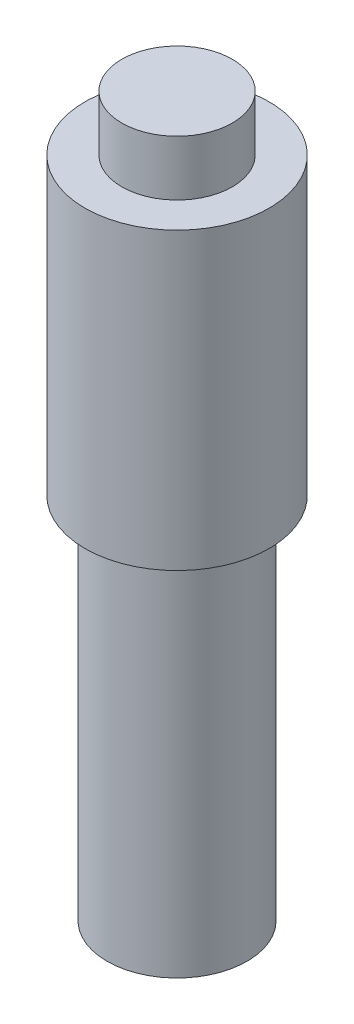
SolidWorks part; units mm, degrees
ref_plane "前基準面" through (0, 0, 0) normal (0, 0, 1) x (1, 0, 0)
ref_plane "上基準面" through (0, 0, 0) normal (0, 1, 0) x (1, 0, 0)
ref_plane "右基準面" through (0, 0, 0) normal (1, 0, 0) x (0, 0, -1)
sketch "草圖1" plane through (0, 0, 0) normal (0, 0, 1) x (1, 0, 0)
  line L0 (0, 46.1554) -> (0, -44.3716) construction
  line L2 (0, 0) -> (3, 0)
  line L3 (0, 0) -> (0, -39)
  line L4 (0, -39) -> (3.8, -39)
  line L5 (5, -3) -> (5, -19)
  line L8 (5, -3) -> (3, -3)
  line L9 (3, 0) -> (3, -3)
  line L11 (3.8, -39) -> (3.8, -19)
  line L12 (3.8, -19) -> (5, -19)
  dimension "D1" = 7.6
  dimension "D2" = 20
  dimension "D3" = 10
  dimension "D4" = 6
  dimension "D5" = 3
  dimension "D6" = 16
revolve "旋轉1" add sketch "草圖1" angle 360 about L0
